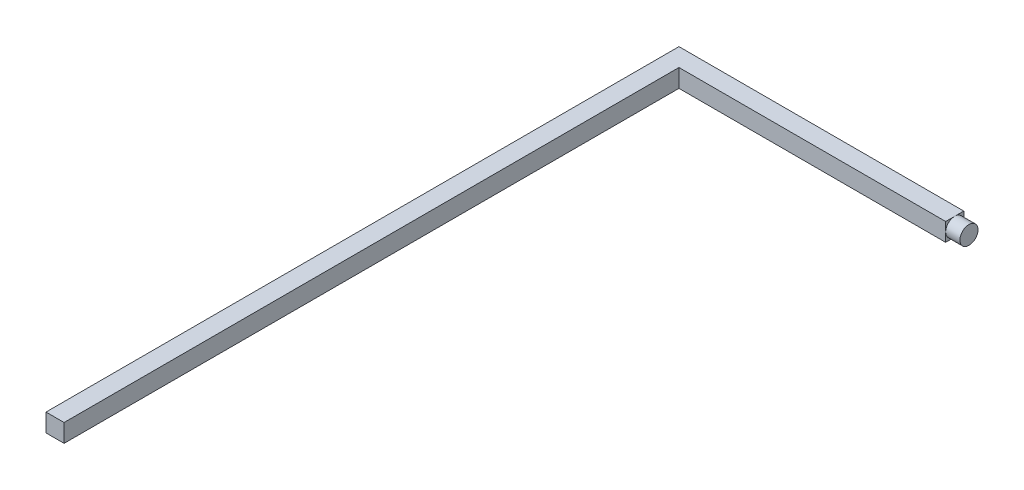
SolidWorks part; units mm, degrees
ref_plane "Front Plane" through (0, 0, 0) normal (0, 0, 1) x (1, 0, 0)
ref_plane "Top Plane" through (0, 0, 0) normal (0, 1, 0) x (1, 0, 0)
ref_plane "Right Plane" through (0, 0, 0) normal (1, 0, 0) x (0, 0, -1)
sketch "Sketch1" plane through (0, 0, 0) normal (0, 1, 0) x (1, 0, 0)
  line L1 (-0.635, -22.225) -> (0.635, -22.225)
  line L2 (-0.635, -22.225) -> (-0.635, 22.225)
  line L3 (-0.635, 22.225) -> (0.635, 22.225)
  line L4 (0.635, -22.225) -> (0.635, 22.225)
  line L5 (-0.635, -22.225) -> (0.635, 22.225) construction
  line L6 (-0.635, 22.225) -> (0.635, -22.225) construction
  line L7 (-0.635, 22.225) -> (19.365, 22.225)
  line L8 (-0.635, 22.225) -> (-0.635, 20.955)
  line L9 (-0.635, 20.955) -> (19.365, 20.955)
  line L10 (19.365, 22.225) -> (19.365, 20.955)
  point P0 (0, 0)
  dimension "D1" = 1.27
  dimension "D2" = 44.45
  dimension "D3" = 1.27
  dimension "D4" = 20
extrude "Boss-Extrude1" add sketch "Sketch1" along normal mid plane 1.27 contours L10 L7 L4 L9 | L2 L9 L4 L3 | L9 L2 L1 L4
sketch "Sketch2" plane through (19.365, 0, 0) normal (1, 0, 0) x (0, 0, -1)
  line L0 (22.225, 0.635) -> (22.225, -0.635) construction
  circle A0 centre (21.59, 0) radius 0.635
  point P4 (22.225, 0)
  dimension "D1" = 1.27
extrude "Boss-Extrude2" add sketch "Sketch2" along normal blind 1
